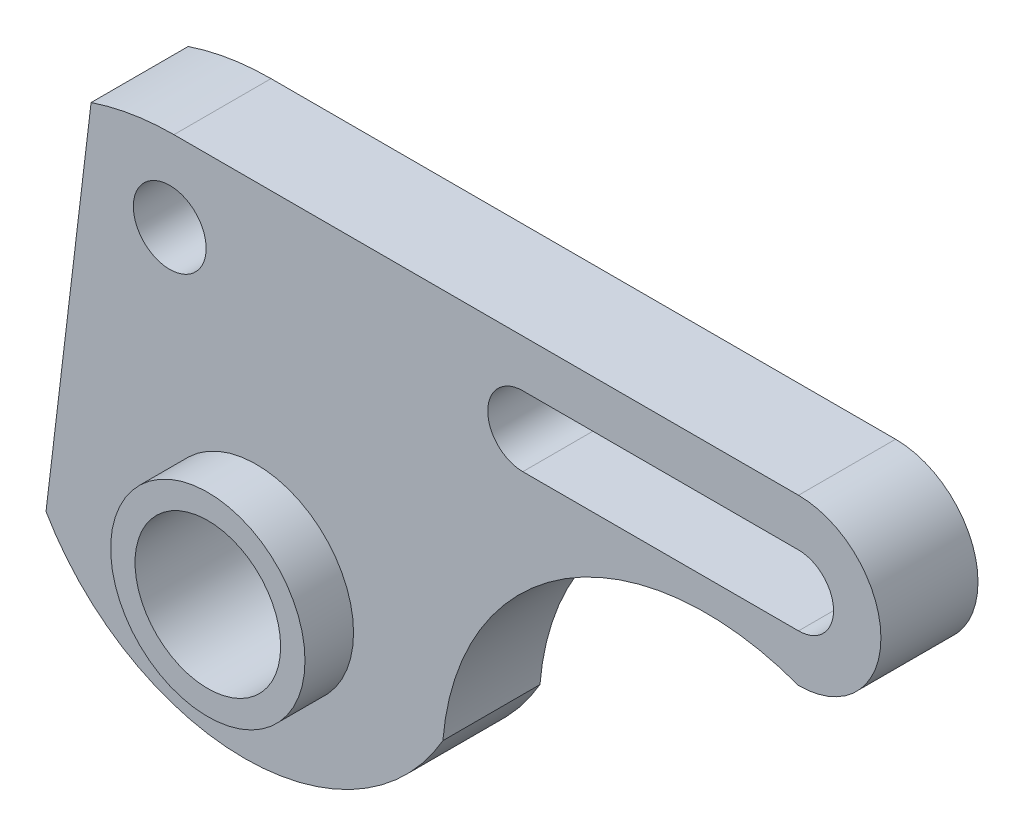
SolidWorks part; units mm, degrees
ref_plane "Front Plane" through (0, 0, 0) normal (0, 0, 1) x (1, 0, 0)
ref_plane "Top Plane" through (0, 0, 0) normal (0, 1, 0) x (1, 0, 0)
ref_plane "Right Plane" through (0, 0, 0) normal (1, 0, 0) x (0, 0, -1)
sketch "Sketch1" plane through (0, 0, 0) normal (0, 0, 1) x (1, 0, 0)
  line L0 (111.7007, 55.4035) -> (-16.9785, 55.4035)
  line L1 (-34.0483, 52.6019) -> (-43.3399, -25.021)
  arc A0 (-43.3399, -25.021) -> (38.425, -25.021) centre (-2.4574, -1.4061) ccw
  arc A1 (38.425, -25.021) -> (111.7007, 21.4465) centre (92.6692, -29.5511) cw
  arc A2 (111.7007, 21.4465) -> (111.7007, 55.4035) centre (111.7007, 38.425) ccw
  arc A3 (-16.9785, 55.4035) -> (-34.0483, 52.6019) centre (-16.9785, 2.0006) ccw
extrude "Boss-Extrude2" add sketch "Sketch1" along normal blind 20
sketch "Sketch3" plane through (0, 0, 20) normal (0, 0, 1) x (1, 0, 0)
  line L0 (54.8956, 38.425) -> (111.7007, 38.425) construction
  line L1 (54.8956, 45.6436) -> (111.7007, 45.6436)
  line L2 (54.8956, 31.2065) -> (111.7007, 31.2065)
  arc A0 (54.8956, 45.6436) -> (54.8956, 31.2065) centre (54.8956, 38.425) ccw
  arc A1 (111.7007, 31.2065) -> (111.7007, 45.6436) centre (111.7007, 38.425) ccw
  circle A2 centre (-17.8489, 38.425) radius 7.5
  point P3 (83.2982, 38.425)
  dimension "D1" = 15
extrude "Cut-Extrude1" cut sketch "Sketch3" against normal blind 20
sketch "Sketch4" plane through (0, 0, 20) normal (0, 0, 1) x (1, 0, 0)
  circle A0 centre (0, -14.9466) radius 20.022
extrude "Boss-Extrude3" add sketch "Sketch4" along normal blind 10
sketch "Sketch5" plane through (0, 0, 30) normal (0, 0, 1) x (1, 0, 0)
  circle A0 centre (0, -14.9466) radius 15
  dimension "D1" = 30
extrude "Cut-Extrude3" cut sketch "Sketch5" against normal blind 40
